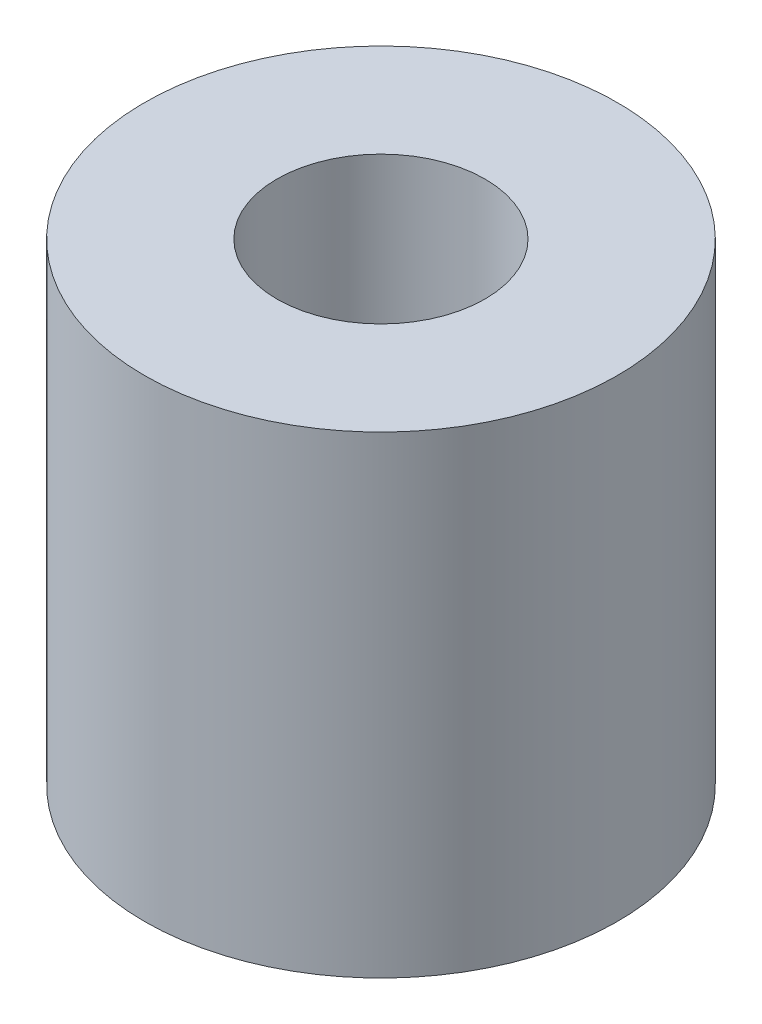
SolidWorks part; units mm, degrees
material "Chrome Stainless Steel"
ref_plane "Спереди" through (0, 0, 0) normal (0, 0, 1) x (1, 0, 0)
ref_plane "Сверху" through (0, 0, 0) normal (0, 1, 0) x (1, 0, 0)
ref_plane "Справа" through (0, 0, 0) normal (1, 0, 0) x (0, 0, -1)
sketch "Sketch1" plane through (0, 0, 0) normal (0, 1, 0) x (1, 0, 0)
  circle A0 centre (0, 0) radius 2.5
  circle A1 centre (0, 0) radius 1.1
  dimension "D1" = 5
  dimension "D2" = 2.2
extrude "Boss-Extrude1" add sketch "Sketch1" along normal blind 5
